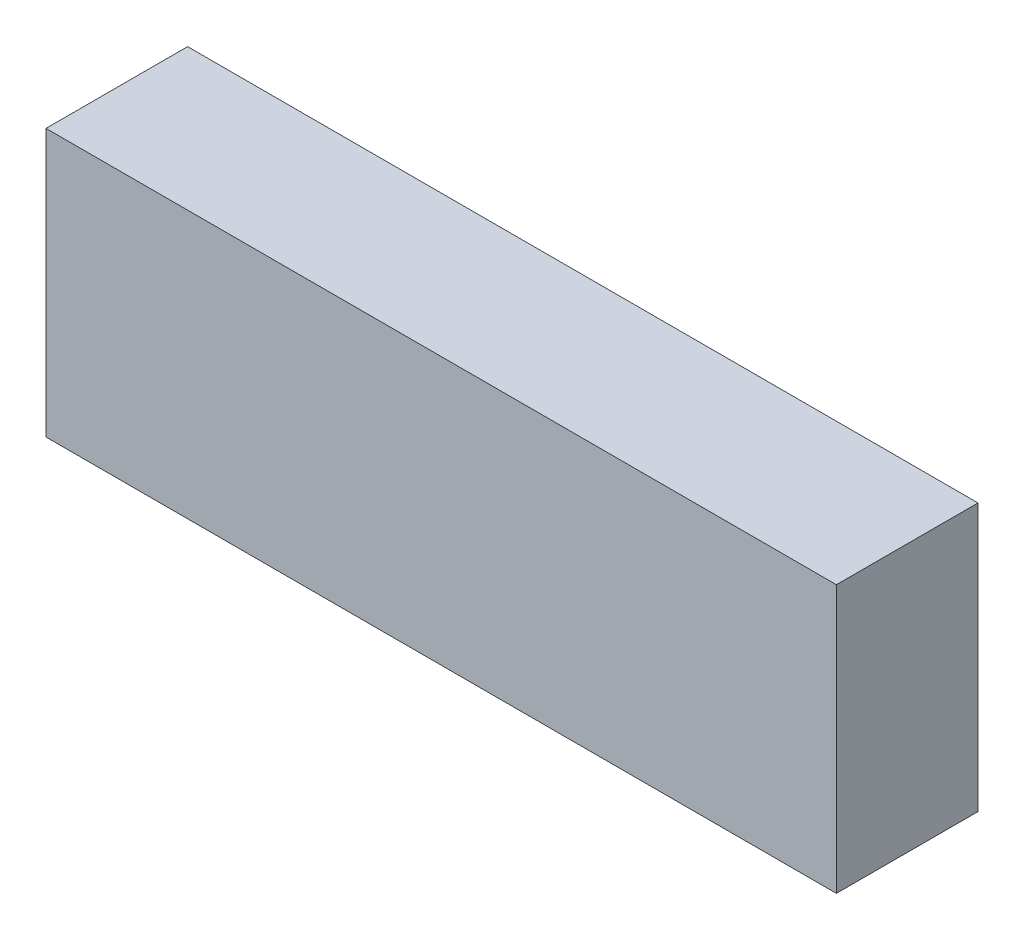
SolidWorks part; units mm, degrees
material "Custom Plastic"
ref_plane "Front Plane" through (0, 0, 0) normal (0, 0, 1) x (1, 0, 0)
ref_plane "Top Plane" through (0, 0, 0) normal (0, 1, 0) x (1, 0, 0)
ref_plane "Right Plane" through (0, 0, 0) normal (1, 0, 0) x (0, 0, -1)
sketch "Sketch1" plane through (0, 0, 0) normal (0, 0, 1) x (1, 0, 0)
  line L1 (-69.469, -23.495) -> (69.469, -23.495)
  line L2 (-69.469, -23.495) -> (-69.469, 23.495)
  line L3 (-69.469, 23.495) -> (69.469, 23.495)
  line L4 (69.469, -23.495) -> (69.469, 23.495)
  line L5 (-69.469, -23.495) -> (69.469, 23.495) construction
  line L6 (-69.469, 23.495) -> (69.469, -23.495) construction
  point P0 (0, 0)
  dimension "D1" = 138.938
  dimension "D2" = 46.99
extrude "Boss-Extrude1" add sketch "Sketch1" along normal blind 24.892
